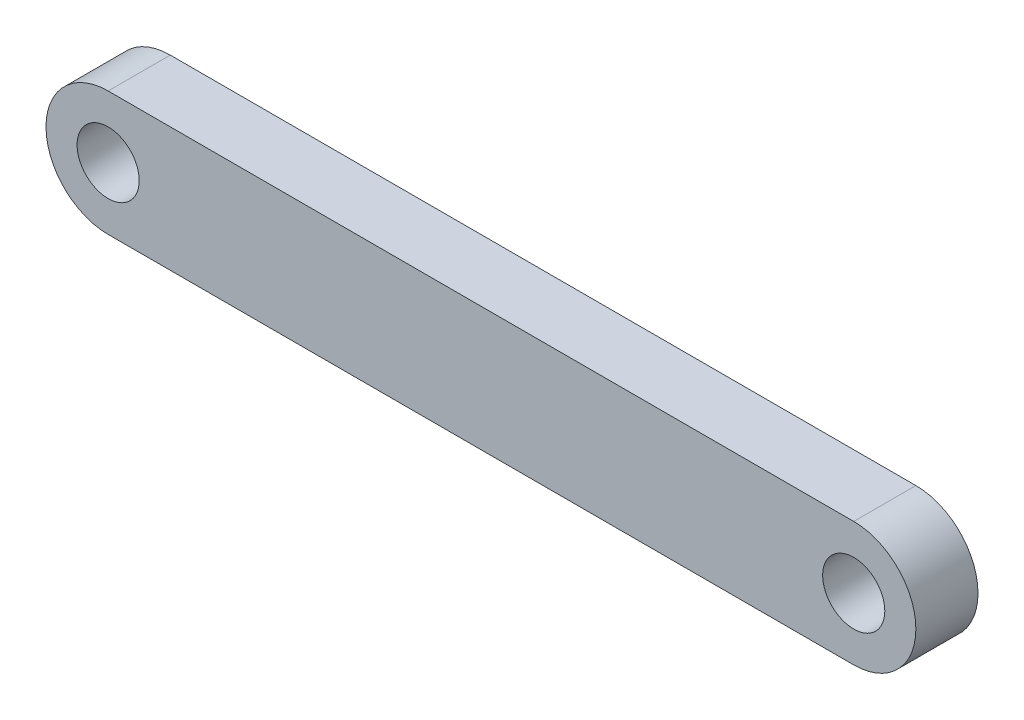
SolidWorks part; units mm, degrees
ref_plane "Front Plane" through (0, 0, 0) normal (0, 0, 1) x (1, 0, 0)
ref_plane "Top Plane" through (0, 0, 0) normal (0, 1, 0) x (1, 0, 0)
ref_plane "Right Plane" through (0, 0, 0) normal (1, 0, 0) x (0, 0, -1)
ref_plane "Plane4"
sketch "Sketch1" plane through (0, 0, 0) normal (0, 0, 1) x (1, 0, 0)
  line L0 (76.2, 12.7) -> (0, 12.7)
  line L1 (0, 0) -> (76.2, 0)
  arc A0 (0, 12.7) -> (0, 0) centre (0, 6.35) ccw
  arc A1 (76.2, 0) -> (76.2, 12.7) centre (76.2, 6.35) ccw
  circle A2 centre (0, 6.35) radius 3.175
  circle A3 centre (76.2, 6.35) radius 3.175
extrude "Extrusion1" add sketch "Sketch1" along normal blind 6.35 contours L1 A1 L0 A0 A3 A2
